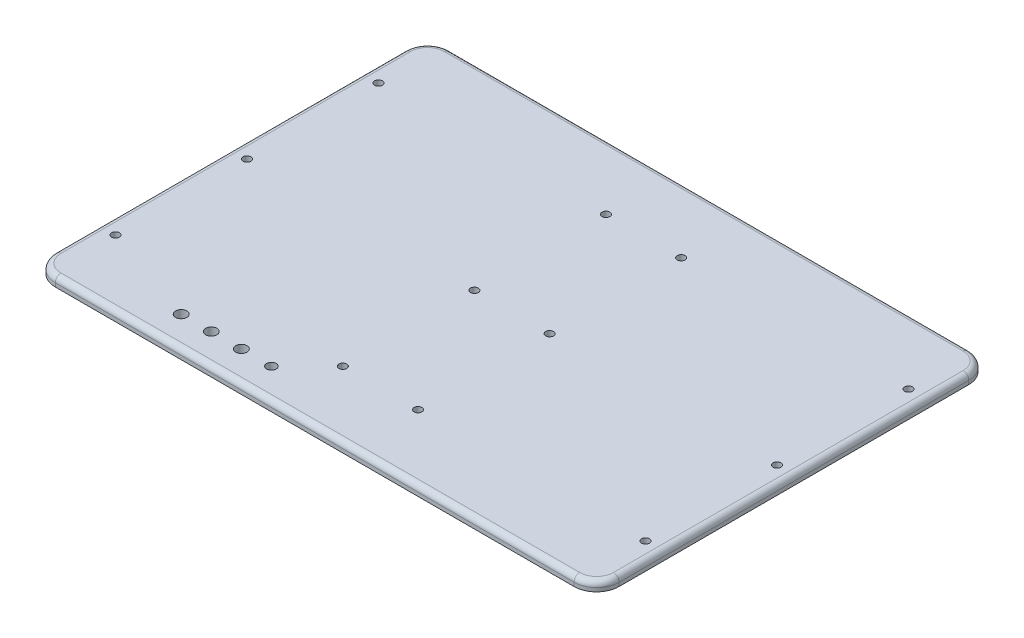
SolidWorks part; units mm, degrees
ref_plane "Front Plane" through (0, 0, 0) normal (0, 0, 1) x (1, 0, 0)
ref_plane "Top Plane" through (0, 0, 0) normal (0, 1, 0) x (1, 0, 0)
ref_plane "Right Plane" through (0, 0, 0) normal (1, 0, 0) x (0, 0, -1)
sketch "Sketch1" plane through (0, 0, 0) normal (0, 1, 0) x (1, 0, 0)
  line L1 (-150, 105) -> (150, 105)
  line L2 (-150, 105) -> (-150, -105)
  line L3 (-150, -105) -> (150, -105)
  line L4 (150, 105) -> (150, -105)
  line L5 (-150, 105) -> (150, -105) construction
  line L6 (-150, -105) -> (150, 105) construction
  point P0 (0, 0)
  dimension "D1" = 300
  dimension "D2" = 210
extrude "Boss-Extrude1" add sketch "Sketch1" along normal blind 5
fillet "Fillet1" radius 12 4 edges at (150, 2.5, -105) (150, 2.5, 105) (-150, 2.5, 105) (-150, 2.5, -105)
sketch "Sketch2" plane through (0, 5, 0) normal (0, 1, 0) x (1, 0, 0)
  line L0 (138, 105) -> (-138, 105) construction
  circle A0 centre (-141, 70) radius 2.075
  circle A1 centre (-141, 0) radius 2.075
  circle A2 centre (-141, -70) radius 2.075
  circle A3 centre (-20, 70) radius 2.075
  circle A4 centre (-20, 0) radius 2.075
  circle A5 centre (-20, -70) radius 2.075
  point P4 (0, 105)
  dimension "D3" = 4.15
  dimension "D1" = 141
  dimension "D2" = 35
  dimension "D5" = 20
  dimension "D4" = 3
extrude "Cut-Extrude1" cut sketch "Sketch2" against normal through all
mirror "Mirror1" about plane through (0, 0, 0) normal (1, 0, 0) of "Cut-Extrude1"
fillet "Fillet2" radius 3 8 edges at (146.4853, 5, -101.4853) (150, 5, 0) (146.4853, 5, 101.4853) (0, 5, 105) (-146.4853, 5, 101.4853) (-150, 5, 0) (-146.4853, 5, -101.4853) (0, 5, -105)
sketch "Sketch3" plane through (0, 5, 0) normal (0, 1, 0) x (1, 0, 0)
  line L0 (-147, 93) -> (-147, -93) construction
  line L1 (-138, -102) -> (138, -102) construction
  circle A0 centre (-87, -89) radius 3
  circle A1 centre (-71, -89) radius 3
  circle A2 centre (-55, -89) radius 3
  circle A4 centre (-39, -89) radius 2.56
  dimension "D1" = 6
  dimension "D5" = 16
  dimension "D6" = 5.12
  dimension "D2" = 60
  dimension "D3" = 13
  dimension "D4" = 3
extrude "Cut-Extrude2" cut sketch "Sketch3" against normal through all
